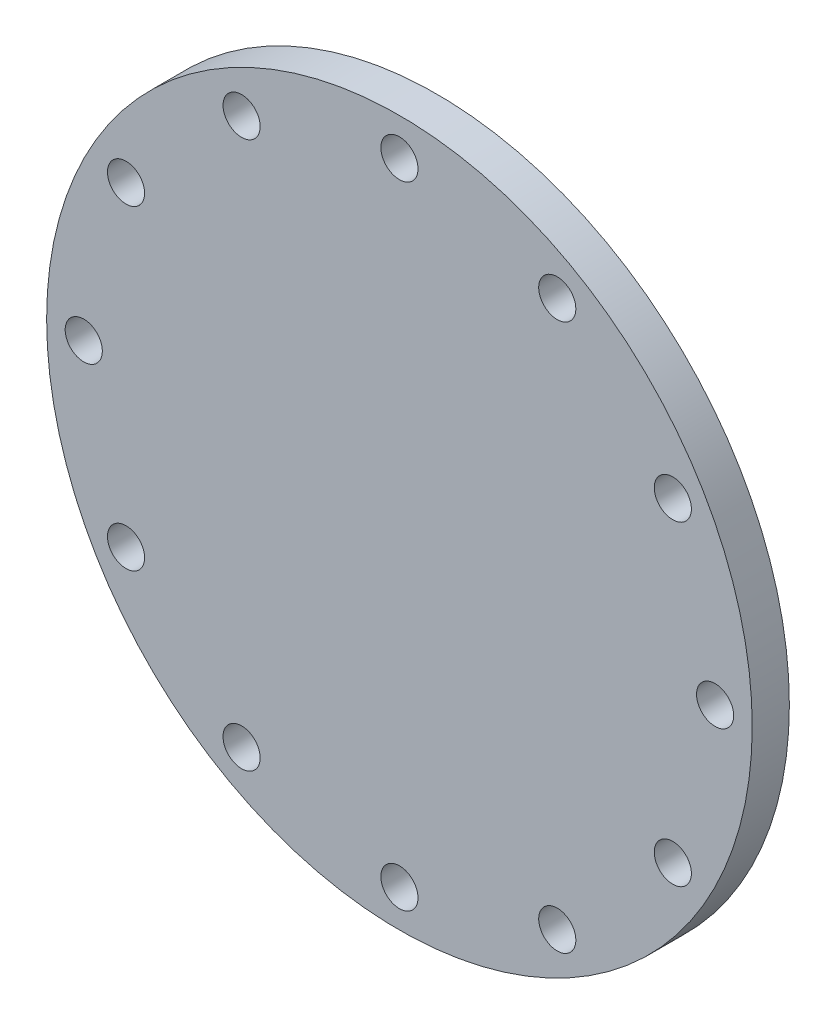
SolidWorks part; units mm, degrees
material "PE High Density"
ref_plane "Front Plane" through (0, 0, 0) normal (0, 0, 1) x (1, 0, 0)
ref_plane "Top Plane" through (0, 0, 0) normal (0, 1, 0) x (1, 0, 0)
ref_plane "Right Plane" through (0, 0, 0) normal (1, 0, 0) x (0, 0, -1)
sketch "Sketch" plane through (0, 0, 0) normal (0, 0, 1) x (1, 0, 0)
  circle A0 centre (0, 0) radius 241.3
  circle A1 centre (0, 0) radius 215.9 construction
  circle A2 centre (0, 215.9) radius 12.7
  circle A3 centre (107.95, 186.9749) radius 12.7
  circle A4 centre (186.9749, 107.95) radius 12.7
  circle A5 centre (215.9, 0) radius 12.7
  circle A6 centre (186.9749, -107.95) radius 12.7
  circle A7 centre (107.95, -186.9749) radius 12.7
  circle A8 centre (0, -215.9) radius 12.7
  circle A9 centre (-107.95, -186.9749) radius 12.7
  circle A10 centre (-186.9749, -107.95) radius 12.7
  circle A11 centre (-215.9, 0) radius 12.7
  circle A12 centre (-186.9749, 107.95) radius 12.7
  circle A13 centre (-107.95, 186.9749) radius 12.7
  point P30 (0, 0)
  dimension "D1" = 431.8
  dimension "D2" = 482.6
  dimension "D3" = 25.4
  dimension "D4" = 12
extrude "Extrude" add sketch "Sketch" along normal blind 25.4
equation "\"BC\"= 17in'dimension found from wolseley (need to confirm with EPG)"
equation "\"T\"= 1in'dimension found from wolseley (need to confirm with EPG)"
equation "\"OD\"= 19in'Made identical to flange ring"
equation "\"D1@Sketch\" = \"BC\""
equation "\"D2@Sketch\" = \"OD\""
equation "\"HD\"= 1in'Made identical to flange ring"
equation "\"D3@Sketch\" = \"HD\""
equation "\"D1@Extrude\"=\"T\""
